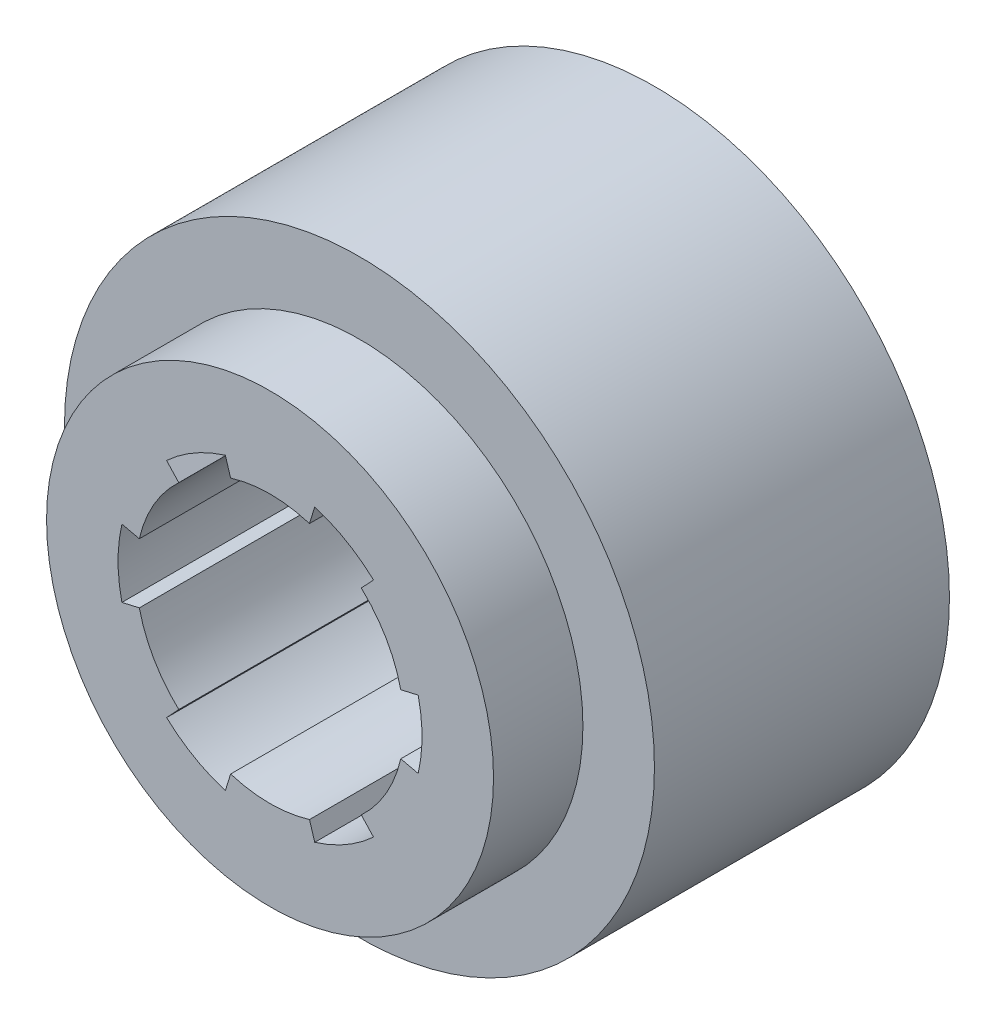
SolidWorks part; units mm, degrees
ref_plane "Ön Düzlem" through (0, 0, 0) normal (0, 0, 1) x (1, 0, 0)
ref_plane "Üst Düzlem" through (0, 0, 0) normal (0, 1, 0) x (1, 0, 0)
ref_plane "Sağ Düzlem" through (0, 0, 0) normal (1, 0, 0) x (0, 0, -1)
sketch "Çizim1" plane through (0, 0, 0) normal (0, 0, 1) x (1, 0, 0)
  line L0 (0, 0) -> (0, 25) construction
  line L1 (-5, 16.2481) -> (-4.4118, 14.3365)
  line L2 (5, 16.2481) -> (4.4118, 14.3365)
  line L3 (-5, 16.2481) -> (-5, 33.2551) construction
  line L4 (5, 16.2481) -> (5, 33.2551) construction
  line L5 (11.5712, 12.4542) -> (10.2099, 10.989)
  line L6 (16.5712, 3.7939) -> (14.6217, 3.3476)
  line L7 (16.5712, -3.7939) -> (14.6217, -3.3476)
  line L8 (11.5712, -12.4542) -> (10.2099, -10.989)
  line L9 (5, -16.2481) -> (4.4118, -14.3365)
  line L10 (-5, -16.2481) -> (-4.4118, -14.3365)
  line L11 (-11.5712, -12.4542) -> (-10.2099, -10.989)
  line L12 (-16.5712, -3.7939) -> (-14.6217, -3.3476)
  line L13 (-16.5712, 3.7939) -> (-14.6217, 3.3476)
  line L14 (-11.5712, 12.4542) -> (-10.2099, 10.989)
  circle A0 centre (0, 0) radius 25
  arc A2 (-10.2099, 10.989) -> (-14.6217, 3.3476) centre (0, 0) ccw
  arc A3 (-16.5712, 3.7939) -> (-16.5712, -3.7939) centre (0, 0) ccw
  circle A4 centre (0, 0) radius 15 construction
  arc A5 (-14.6217, -3.3476) -> (-10.2099, -10.989) centre (0, 0) ccw
  arc A6 (-4.4118, -14.3365) -> (4.4118, -14.3365) centre (0, 0) ccw
  circle A7 centre (0, 0) radius 17 construction
  arc A8 (-11.5712, -12.4542) -> (-5, -16.2481) centre (0, 0) ccw
  arc A9 (5, -16.2481) -> (11.5712, -12.4542) centre (0, 0) ccw
  arc A10 (10.2099, -10.989) -> (14.6217, -3.3476) centre (0, 0) ccw
  arc A11 (16.5712, -3.7939) -> (16.5712, 3.7939) centre (0, 0) ccw
  arc A12 (14.6217, 3.3476) -> (10.2099, 10.989) centre (0, 0) ccw
  arc A13 (11.5712, 12.4542) -> (5, 16.2481) centre (0, 0) ccw
  arc A14 (4.4118, 14.3365) -> (-4.4118, 14.3365) centre (0, 0) ccw
  arc A15 (-5, 16.2481) -> (-11.5712, 12.4542) centre (0, 0) ccw
  point P39 (0, 0)
  dimension "D1" = 50
  dimension "D4" = 10
  dimension "D5" = 5
  dimension "D2" = 10
  dimension "D3" = 8
  dimension "D6" = 6
extrude "Yükseklik-Ekstrüzyon1" add sketch "Çizim1" along normal mid plane 10
sketch "Çizim2" plane through (0, 0, -5) normal (0, 0, -1) x (-1, 0, 0)
  line L0 (-5, 16.2481) -> (-4.4118, 14.3365) construction
  line L1 (4.4118, 14.3365) -> (5, 16.2481) construction
  line L2 (11.5712, 12.4542) -> (10.2099, 10.989) construction
  line L3 (14.6217, 3.3476) -> (16.5712, 3.7939) construction
  line L4 (16.5712, -3.7939) -> (14.6217, -3.3476) construction
  line L5 (10.2099, -10.989) -> (11.5712, -12.4542) construction
  line L6 (5, -16.2481) -> (4.4118, -14.3365) construction
  line L7 (-4.4118, -14.3365) -> (-5, -16.2481) construction
  line L8 (-11.5712, -12.4542) -> (-10.2099, -10.989) construction
  line L9 (-14.6217, -3.3476) -> (-16.5712, -3.7939) construction
  line L10 (-16.5712, 3.7939) -> (-14.6217, 3.3476) construction
  line L11 (-10.2099, 10.989) -> (-11.5712, 12.4542) construction
  line L12 (-5, 16.2481) -> (-4.4118, 14.3365)
  line L13 (4.4118, 14.3365) -> (5, 16.2481)
  line L14 (11.5712, 12.4542) -> (10.2099, 10.989)
  line L15 (14.6217, 3.3476) -> (16.5712, 3.7939)
  line L16 (16.5712, -3.7939) -> (14.6217, -3.3476)
  line L17 (10.2099, -10.989) -> (11.5712, -12.4542)
  line L18 (5, -16.2481) -> (4.4118, -14.3365)
  line L19 (-4.4118, -14.3365) -> (-5, -16.2481)
  line L20 (-11.5712, -12.4542) -> (-10.2099, -10.989)
  line L21 (-14.6217, -3.3476) -> (-16.5712, -3.7939)
  line L22 (-16.5712, 3.7939) -> (-14.6217, 3.3476)
  line L23 (-10.2099, 10.989) -> (-11.5712, 12.4542)
  circle A0 centre (0, 0) radius 33
  arc A1 (4.4118, 14.3365) -> (-4.4118, 14.3365) centre (0, 0) ccw construction
  arc A3 (11.5712, 12.4542) -> (5, 16.2481) centre (0, 0) ccw construction
  arc A4 (14.6217, 3.3476) -> (10.2099, 10.989) centre (0, 0) ccw construction
  arc A5 (16.5712, -3.7939) -> (16.5712, 3.7939) centre (0, 0) ccw construction
  arc A6 (10.2099, -10.989) -> (14.6217, -3.3476) centre (0, 0) ccw construction
  arc A7 (5, -16.2481) -> (11.5712, -12.4542) centre (0, 0) ccw construction
  arc A8 (-4.4118, -14.3365) -> (4.4118, -14.3365) centre (0, 0) ccw construction
  arc A9 (-11.5712, -12.4542) -> (-5, -16.2481) centre (0, 0) ccw construction
  arc A10 (-14.6217, -3.3476) -> (-10.2099, -10.989) centre (0, 0) ccw construction
  arc A11 (-16.5712, 3.7939) -> (-16.5712, -3.7939) centre (0, 0) ccw construction
  arc A12 (-10.2099, 10.989) -> (-14.6217, 3.3476) centre (0, 0) ccw construction
  arc A13 (-5, 16.2481) -> (-11.5712, 12.4542) centre (0, 0) ccw construction
  arc A14 (4.4118, 14.3365) -> (-4.4118, 14.3365) centre (0, 0) ccw
  arc A15 (11.5712, 12.4542) -> (5, 16.2481) centre (0, 0) ccw
  arc A16 (14.6217, 3.3476) -> (10.2099, 10.989) centre (0, 0) ccw
  arc A17 (16.5712, -3.7939) -> (16.5712, 3.7939) centre (0, 0) ccw
  arc A18 (10.2099, -10.989) -> (14.6217, -3.3476) centre (0, 0) ccw
  arc A19 (5, -16.2481) -> (11.5712, -12.4542) centre (0, 0) ccw
  arc A20 (-4.4118, -14.3365) -> (4.4118, -14.3365) centre (0, 0) ccw
  arc A21 (-11.5712, -12.4542) -> (-5, -16.2481) centre (0, 0) ccw
  arc A22 (-14.6217, -3.3476) -> (-10.2099, -10.989) centre (0, 0) ccw
  arc A23 (-16.5712, 3.7939) -> (-16.5712, -3.7939) centre (0, 0) ccw
  arc A24 (-10.2099, 10.989) -> (-14.6217, 3.3476) centre (0, 0) ccw
  arc A25 (-5, 16.2481) -> (-11.5712, 12.4542) centre (0, 0) ccw
  dimension "D1" = 66
extrude "Yükseklik-Ekstrüzyon2" add sketch "Çizim2" along normal blind 33
sketch "Çizim3" plane through (0, 0, 0) normal (0, 1, 0) x (1, 0, 0)
  line L0 (30.7721, 111.9509) -> (30.7721, 70.4678)
  line L1 (-24.2279, 111.3784) -> (-24.2279, 70.4678)
  arc A0 (30.7721, 70.4678) -> (-24.2279, 70.4678) centre (3.2721, 133.6504) cw
  point P5 (30.7721, 91.2093)
  point P6 (-24.2279, 70.4678)
  dimension "D1" = 55
